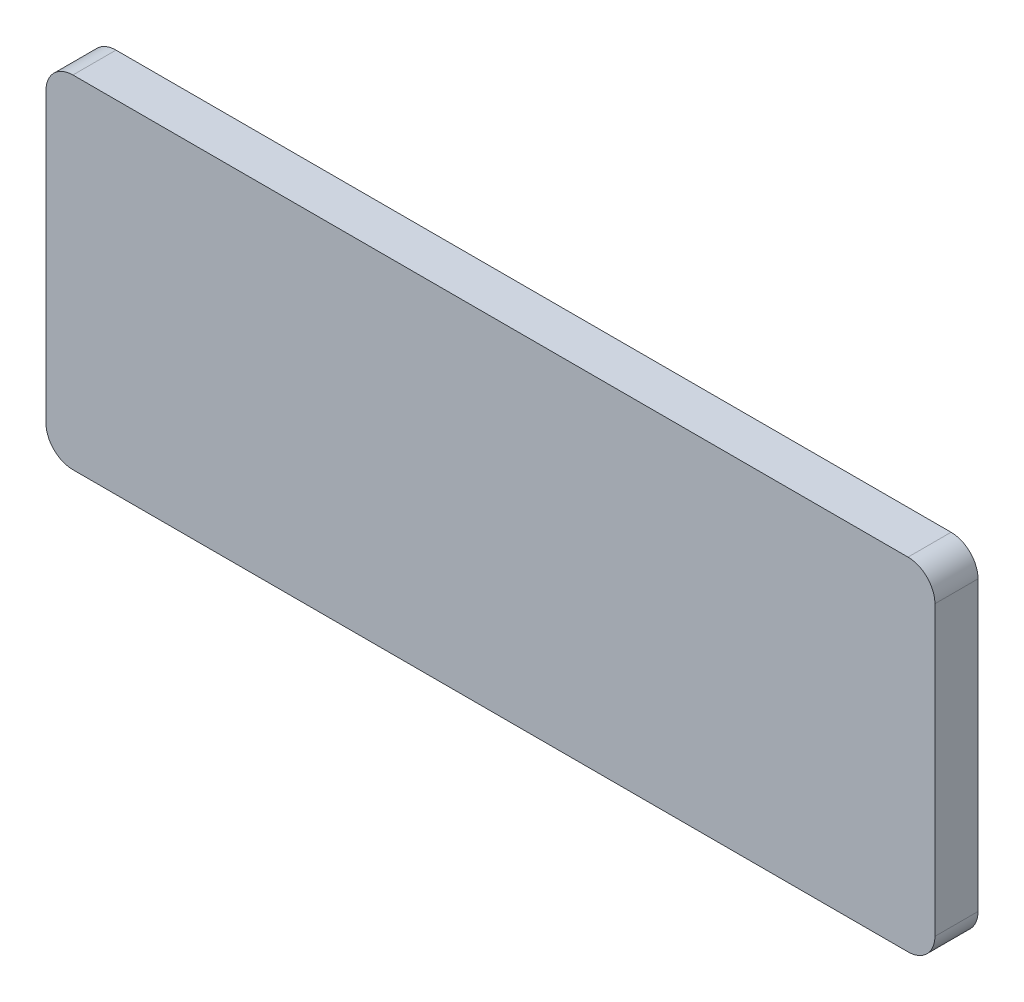
SolidWorks part; units mm, degrees
ref_plane "Front Plane" through (0, 0, 0) normal (0, 0, 1) x (1, 0, 0)
ref_plane "Top Plane" through (0, 0, 0) normal (0, 1, 0) x (1, 0, 0)
ref_plane "Right Plane" through (0, 0, 0) normal (1, 0, 0) x (0, 0, -1)
sketch "草图1" plane through (0, 0, 0) normal (0, 0, 1) x (1, 0, 0)
  line L1 (16.51, -6.35) -> (-16.51, -6.35)
  line L2 (16.51, -6.35) -> (16.51, 6.35)
  line L3 (16.51, 6.35) -> (-16.51, 6.35)
  line L4 (-16.51, -6.35) -> (-16.51, 6.35)
  line L5 (16.51, -6.35) -> (-16.51, 6.35) construction
  line L6 (16.51, 6.35) -> (-16.51, -6.35) construction
  point P0 (0, 0)
  dimension "D1" = 33.02
  dimension "D2" = 12.7
extrude "凸台-拉伸1" add sketch "草图1" along normal blind 1.6
fillet "圆角1" radius 1 4 edges at (-16.51, -6.35, 0.8) (16.51, -6.35, 0.8) (16.51, 6.35, 0.8) (-16.51, 6.35, 0.8)
